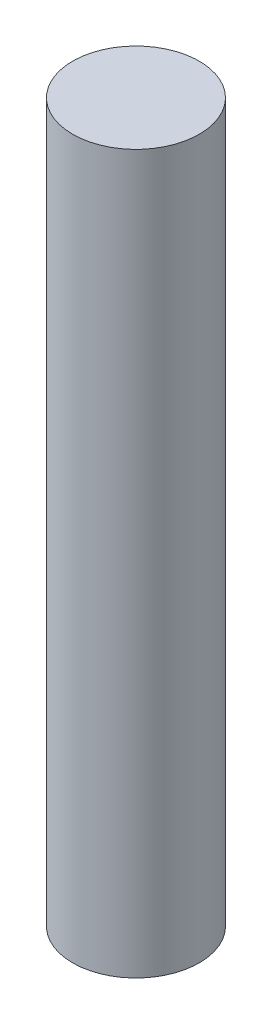
SolidWorks part; units mm, degrees
ref_plane "Front Plane" through (0, 0, 0) normal (0, 0, 1) x (1, 0, 0)
ref_plane "Top Plane" through (0, 0, 0) normal (0, 1, 0) x (1, 0, 0)
ref_plane "Right Plane" through (0, 0, 0) normal (1, 0, 0) x (0, 0, -1)
sketch "Sketch1" plane through (0, 0, 0) normal (0, 1, 0) x (1, 0, 0)
  circle A0 centre (0, 0) radius 7.5
  dimension "D1" = 15
extrude "Boss-Extrude1" add sketch "Sketch1" along normal blind 85
